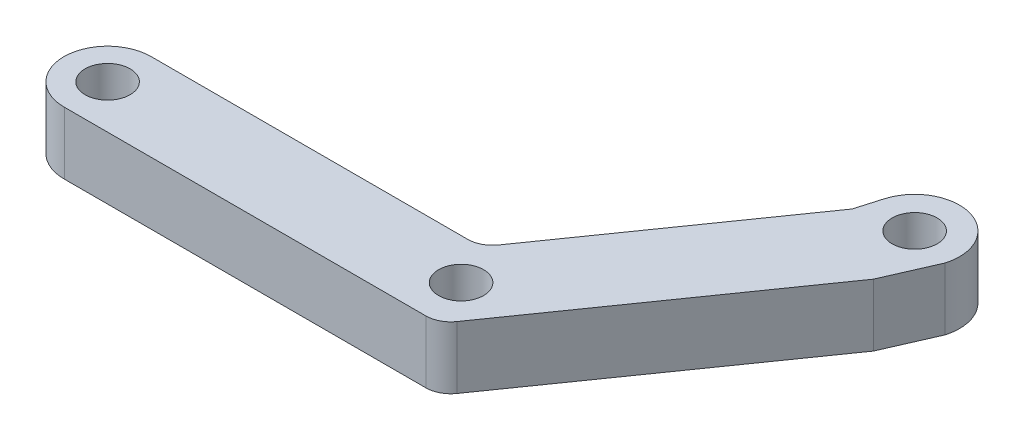
SolidWorks part; units mm, degrees
ref_plane "Front Plane" through (0, 0, 0) normal (0, 0, 1) x (1, 0, 0)
ref_plane "Top Plane" through (0, 0, 0) normal (0, 1, 0) x (1, 0, 0)
ref_plane "Right Plane" through (0, 0, 0) normal (1, 0, 0) x (0, 0, -1)
sketch "Sketch1" plane through (0, 0, 0) normal (0, 1, 0) x (1, 0, 0)
  line L0 (0.0482, 4.445) -> (32.2504, 4.445)
  line L1 (34.331, 5.5281) -> (49.1592, 26.705)
  line L2 (0.0482, -4.445) -> (36.8782, -4.445)
  line L3 (38.9589, -3.3619) -> (56.4415, 21.6059)
  line L4 (49.1592, 26.705) -> (56.4415, 21.6059) construction
  line L5 (38.0511, -4.158) -> (33.4232, 4.732) construction
  line L6 (0.0482, 4.445) -> (33.5726, 4.445) construction
  line L7 (33.5726, 4.445) -> (49.1592, 26.705) construction
  line L8 (0.0482, -4.445) -> (38.2005, -4.445) construction
  line L9 (38.2005, -4.445) -> (56.4415, 21.6059) construction
  line L10 (56.4415, 21.6059) -> (58.6648, 26.6859)
  line L11 (49.1592, 26.705) -> (49.9009, 29.245)
  line L12 (58.6648, 26.6859) -> (49.9009, 29.245) construction
  arc A0 (0.0482, 4.445) -> (0.0482, -4.445) centre (0, 0) ccw
  arc A1 (49.9009, 29.245) -> (58.6648, 26.6859) centre (54.2829, 27.9654) cw
  arc A2 (32.2504, 4.445) -> (34.331, 5.5281) centre (32.2504, 6.985) ccw
  circle A3 centre (0, 0) radius 2.2924
  circle A4 centre (35.7371, 0.287) radius 2.2923
  arc A5 (36.8782, -4.445) -> (38.9589, -3.3619) centre (36.8782, -1.905) ccw
  circle A7 centre (54.2829, 27.9654) radius 2.2923
  point P12 (49.5301, 27.975)
  point P22 (57.5532, 24.1459)
  dimension "D1" = 2.54
  dimension "D4" = 8.89
  dimension "D5" = 4.5847
  dimension "D7" = 4.4453
  dimension "D8" = 125
  dimension "D10" = 2.54
  dimension "D12" = 4.5847
  dimension "D11" = 4.5847
  dimension "D3" = 36.83
  dimension "D6" = 30.48
  dimension "D9" = 5.08
  dimension "D2" = 8.89
extrude "Boss-Extrude1" add sketch "Sketch1" along normal blind 6.35
